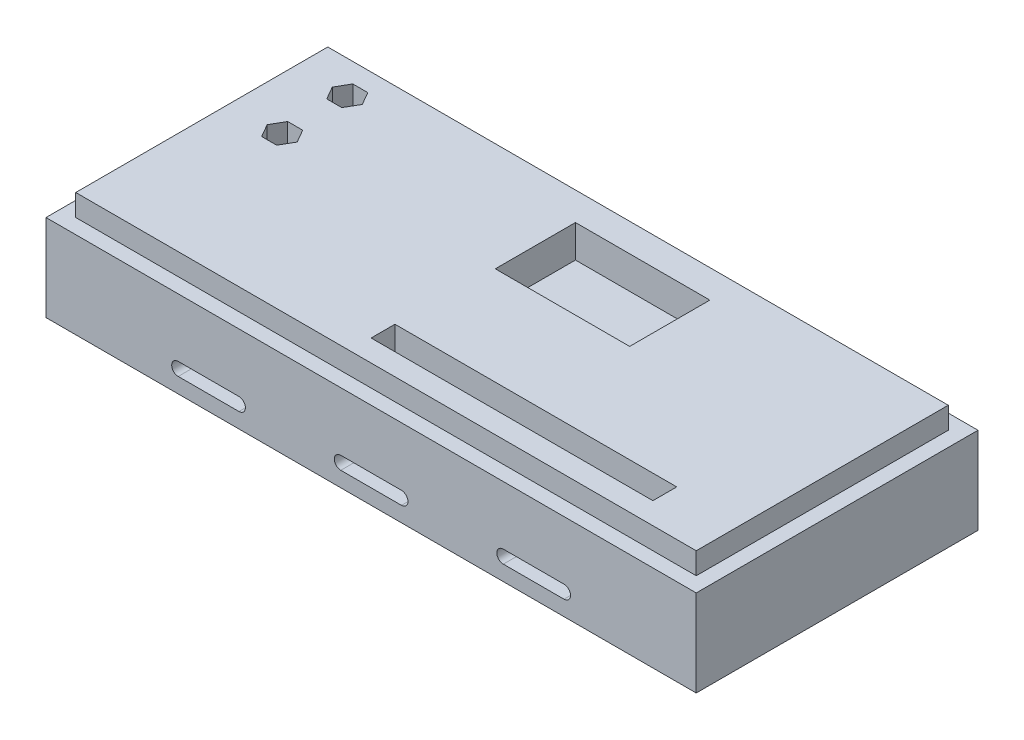
SolidWorks part; units mm, degrees
ref_plane "Front Plane" through (0, 0, 0) normal (0, 0, 1) x (1, 0, 0)
ref_plane "Top Plane" through (0, 0, 0) normal (0, 1, 0) x (1, 0, 0)
ref_plane "Right Plane" through (0, 0, 0) normal (1, 0, 0) x (0, 0, -1)
sketch "Sketch1" plane through (0, 0, 0) normal (0, 1, 0) x (1, 0, 0)
  line L1 (-75, -32.5) -> (75, -32.5)
  line L2 (-75, -32.5) -> (-75, 32.5)
  line L3 (-75, 32.5) -> (75, 32.5)
  line L4 (75, -32.5) -> (75, 32.5)
  line L5 (-75, -32.5) -> (75, 32.5) construction
  line L6 (-75, 32.5) -> (75, -32.5) construction
  point P1 (0, 0)
  dimension "D1" = 150
  dimension "D2" = 65
extrude "Boss-Extrude1" add sketch "Sketch1" along normal blind 20
sketch "Sketch2" plane through (0, 0, 32.5) normal (0, 0, 1) x (1, 0, 0)
  line L0 (0, 0) -> (0, 20) construction
  line L1 (-75, 20) -> (75, 20) construction
  line L2 (0, 10) -> (-75, 10) construction
  line L3 (-75, 20) -> (-75, 0) construction
  line L4 (0, 10) -> (75, 10) construction
  line L5 (-44.5, 5) -> (-30.5, 5) construction
  line L6 (-37.5, 10) -> (-37.5, 0) construction
  line L7 (55, 0) -> (-55, 0) construction
  line L8 (75, 20) -> (75, 0) construction
  line L9 (37.5, 10) -> (37.5, 0) construction
  line L10 (-7, 5) -> (7, 5) construction
  line L11 (-7, 6.5) -> (7, 6.5)
  line L12 (-7, 3.5) -> (7, 3.5)
  line L13 (-44.5, 6.5) -> (-30.5, 6.5)
  line L14 (-44.5, 3.5) -> (-30.5, 3.5)
  line L15 (30.5, 5) -> (44.5, 5) construction
  line L16 (30.5, 6.5) -> (44.5, 6.5)
  line L17 (30.5, 3.5) -> (44.5, 3.5)
  arc A0 (-7, 6.5) -> (-7, 3.5) centre (-7, 5) ccw
  arc A1 (7, 3.5) -> (7, 6.5) centre (7, 5) ccw
  arc A2 (-44.5, 6.5) -> (-44.5, 3.5) centre (-44.5, 5) ccw
  arc A3 (-30.5, 3.5) -> (-30.5, 6.5) centre (-30.5, 5) ccw
  arc A4 (30.5, 6.5) -> (30.5, 3.5) centre (30.5, 5) ccw
  arc A5 (44.5, 3.5) -> (44.5, 6.5) centre (44.5, 5) ccw
  point P20 (0, 5)
  point P29 (-37.5, 5)
  point P37 (37.5, 5)
  dimension "D1" = 14
  dimension "D2" = 3
  dimension "D3" = 3.5
  dimension "D4" = 14
  dimension "D5" = 3
  dimension "D6" = 3.5
  dimension "D7" = 14
  dimension "D8" = 3
  dimension "D9" = 3.5
extrude "Cut-Extrude1" cut sketch "Sketch2" against normal through all
sketch "Sketch3" plane through (0, 20, 0) normal (0, 1, 0) x (1, 0, 0)
  line L1 (-71.571, -29.071) -> (71.571, -29.071)
  line L2 (-71.571, -29.071) -> (-71.571, 29.071)
  line L3 (-71.571, 29.071) -> (71.571, 29.071)
  line L4 (71.571, -29.071) -> (71.571, 29.071)
  line L5 (-71.571, -29.071) -> (71.571, 29.071) construction
  line L6 (-71.571, 29.071) -> (71.571, -29.071) construction
  line L7 (-75, 32.5) -> (-75, -32.5) construction
  line L8 (75, 32.5) -> (-75, 32.5) construction
  point P0 (0, 0)
  dimension "D1" = 3.429
  dimension "D2" = 3.429
extrude "Boss-Extrude2" add sketch "Sketch3" along normal blind 5
sketch "Sketch4" plane through (0, 25, 0) normal (0, 1, 0) x (1, 0, 0)
  line L0 (-59.571, 21.571) -> (-59.571, 6.551) construction
  line L1 (71.571, 29.071) -> (-71.571, 29.071) construction
  line L2 (-71.571, 29.071) -> (-71.571, -29.071) construction
  line L4 (-61.3031, 24.571) -> (-63.0351, 21.571)
  line L5 (-63.0351, 21.571) -> (-61.3031, 18.571)
  line L6 (-61.3031, 18.571) -> (-57.8389, 18.571)
  line L7 (-57.8389, 18.571) -> (-56.1069, 21.571)
  line L8 (-56.1069, 21.571) -> (-57.8389, 24.571)
  line L9 (-57.8389, 24.571) -> (-61.3031, 24.571)
  line L10 (-61.3031, 9.551) -> (-63.0351, 6.551)
  line L11 (-63.0351, 6.551) -> (-61.3031, 3.551)
  line L12 (-61.3031, 3.551) -> (-57.8389, 3.551)
  line L13 (-57.8389, 3.551) -> (-56.1069, 6.551)
  line L14 (-56.1069, 6.551) -> (-57.8389, 9.551)
  line L15 (-57.8389, 9.551) -> (-61.3031, 9.551)
  circle A2 centre (-59.571, 21.571) radius 3 construction
  circle A3 centre (-59.571, 6.551) radius 3 construction
  dimension "D3" = 6
  dimension "D4" = 6
  dimension "D1" = 15.02
  dimension "D2" = 7.5
  dimension "D5" = 12
sketch "Sketch5" plane through (0, 25, 0) normal (0, 1, 0) x (1, 0, 0)
  line L1 (-61.591, 4.541) -> (-29.841, 4.541)
  line L2 (-61.591, 4.541) -> (-61.591, 23.591)
  line L3 (-61.591, 23.591) -> (-29.841, 23.591)
  line L4 (-29.841, 4.541) -> (-29.841, 23.591)
  line L5 (-61.591, 4.541) -> (-29.841, 23.591) construction
  line L6 (-61.591, 23.591) -> (-29.841, 4.541) construction
  point P0 (-45.716, 14.066)
  dimension "D3" = 2.02
  dimension "D1" = 19.05
  dimension "D2" = 31.75
  dimension "D4" = 2.02
extrude "Cut-Extrude2" cut sketch "Sketch4" against normal blind 6.5
sketch "Sketch6" plane through (0, 25, 0) normal (0, 1, 0) x (1, 0, 0)
  line L0 (-71.571, -29.071) -> (71.571, -29.071) construction
  line L1 (-8.429, -24.071) -> (56.571, -24.071)
  line L2 (-8.429, -24.071) -> (-8.429, -18.571)
  line L3 (-8.429, -18.571) -> (56.571, -18.571)
  line L4 (56.571, -24.071) -> (56.571, -18.571)
  line L5 (-8.429, -24.071) -> (56.571, -18.571) construction
  line L6 (-8.429, -18.571) -> (56.571, -24.071) construction
  line L7 (71.571, -29.071) -> (71.571, 29.071) construction
  point P0 (24.071, -21.321)
  dimension "D1" = 5.5
  dimension "D2" = 65
  dimension "D3" = 5
  dimension "D4" = 15
extrude "Cut-Extrude3" cut sketch "Sketch6" against normal blind 10
sketch "Sketch7" plane through (0, 25, 0) normal (0, 1, 0) x (1, 0, 0)
  line L0 (71.571, 29.071) -> (-71.571, 29.071) construction
  line L1 (-7.929, 4.071) -> (23.071, 4.071)
  line L2 (-7.929, 4.071) -> (-7.929, 22.571)
  line L3 (-7.929, 22.571) -> (23.071, 22.571)
  line L4 (23.071, 4.071) -> (23.071, 22.571)
  line L5 (-7.929, 4.071) -> (23.071, 22.571) construction
  line L6 (-7.929, 22.571) -> (23.071, 4.071) construction
  line L7 (71.571, -29.071) -> (71.571, 29.071) construction
  point P0 (7.571, 13.321)
  dimension "D1" = 31
  dimension "D2" = 18.5
  dimension "D3" = 6.5
  dimension "D4" = 48.5
extrude "Cut-Extrude4" cut sketch "Sketch7" against normal blind 7.5
